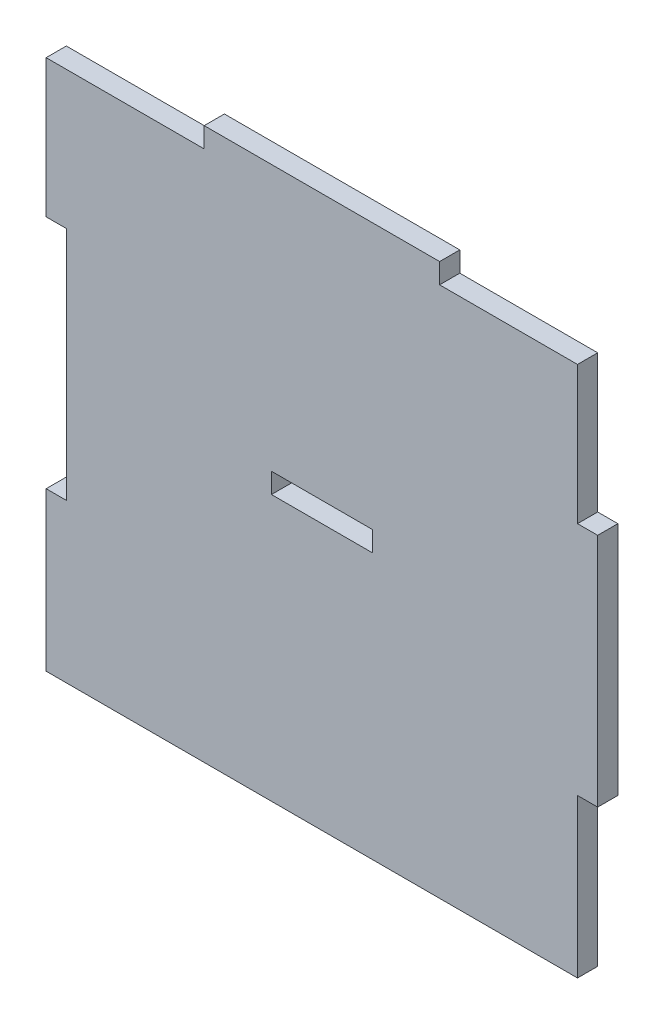
SolidWorks part; units mm, degrees
ref_plane "Front Plane" through (0, 0, 0) normal (0, 0, 1) x (1, 0, 0)
ref_plane "Top Plane" through (0, 0, 0) normal (0, 1, 0) x (1, 0, 0)
ref_plane "Right Plane" through (0, 0, 0) normal (1, 0, 0) x (0, 0, -1)
sketch "Sketch1" plane through (0, 0, 0) normal (0, 0, 1) x (1, 0, 0)
  line L0 (0, 38) -> (0, -39.5) construction
  line L5 (-38, 39.5) -> (-17.5, 39.5)
  line L6 (-38, 16) -> (-38, -16)
  line L24 (38, 39.5) -> (38, 19)
  line L26 (-41, -39.5) -> (38, -39.5)
  line L27 (-38, 0) -> (38, 0) construction
  line L28 (-17.5, 39.5) -> (-17.5, 42.5)
  line L29 (-17.5, 42.5) -> (17.5, 42.5)
  line L30 (17.5, 42.5) -> (17.5, 39.5)
  line L33 (-41, 19) -> (-41, 39.5)
  line L34 (-41, 39.5) -> (-38, 39.5)
  line L35 (-41, -19) -> (-41, -39.5)
  line L36 (38, -19) -> (38, -39.5)
  line L43 (41, 16) -> (41, -16)
  line L44 (-38, 16) -> (-38, 19)
  line L46 (17.5, 39.5) -> (38, 39.5)
  line L48 (-38, 19) -> (-41, 19)
  line L50 (-41, -19) -> (-41, -16)
  line L51 (-41, -16) -> (-38, -16)
  line L52 (38, -19) -> (38, -16)
  line L53 (38, -16) -> (41, -16)
  line L54 (41, 16) -> (41, 19)
  line L55 (41, 19) -> (38, 19)
  point P0 (0, 0)
  dimension "D1" = 79
  dimension "D2" = 76
  dimension "D3" = 3
  dimension "D4" = 35
  dimension "D5" = 3
  dimension "D6" = 76
  dimension "D7" = 35
  dimension "D8" = 3
  dimension "D9" = 3
  dimension "D10" = 3
  dimension "D11" = 3
  dimension "D12" = 35
  dimension "D13" = 0
  dimension "D14" = 20.5
extrude "Boss-Extrude1" add sketch "Sketch1" along normal blind 3
sketch "Sketch2" plane through (0, 0, 3) normal (0, 0, 1) x (1, 0, 0)
  line L0 (-41, -39.5) -> (38, -39.5) construction
  line L5 (-7.5, 3) -> (7.5, 3)
  line L6 (-7.5, 3) -> (-7.5, 0)
  line L7 (-7.5, 0) -> (7.5, 0)
  line L8 (7.5, 3) -> (7.5, 0)
  line L9 (-7.5, 3) -> (7.5, 0) construction
  line L10 (-7.5, 0) -> (7.5, 3) construction
  point P0 (0, 0)
  point P1 (0, 1.5)
  dimension "D1" = 15
  dimension "D2" = 3
  dimension "D3" = 0
  dimension "D4" = 41
extrude "Cut-Extrude1" cut sketch "Sketch2" against normal blind 3
